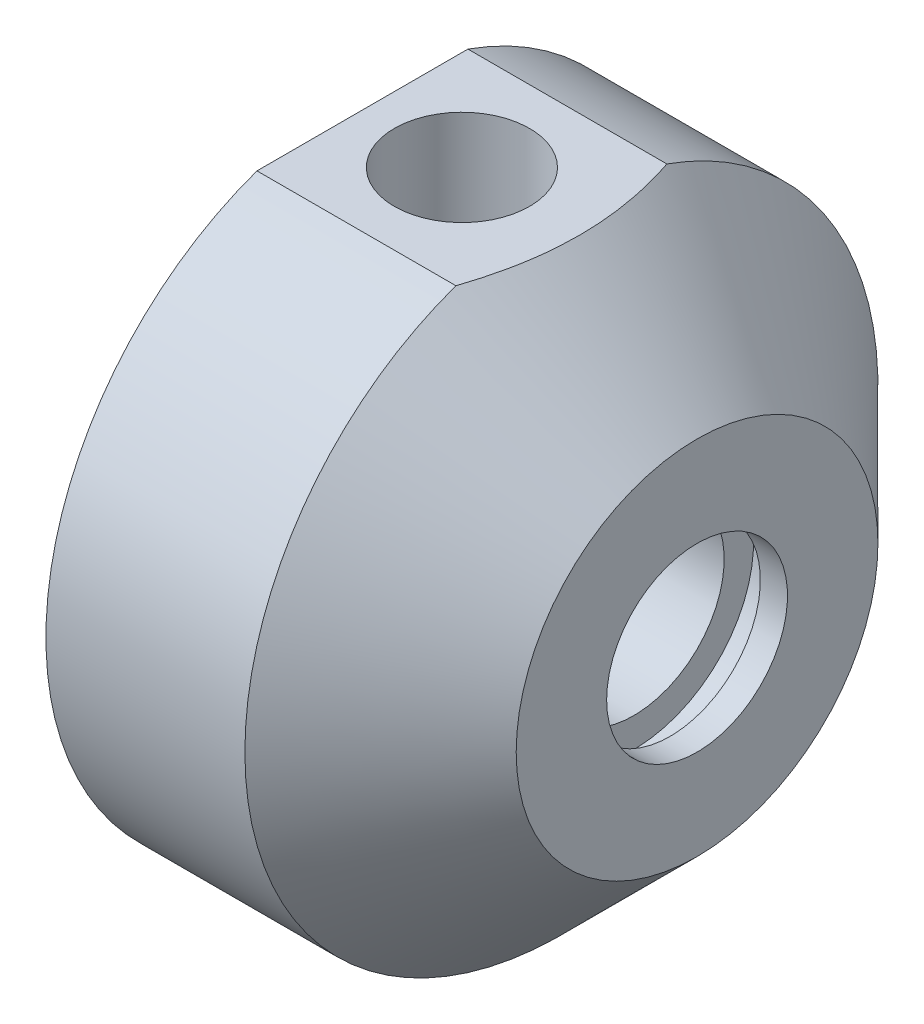
SolidWorks part; units mm, degrees
ref_plane "Plan1" through (0, 0, 0) normal (0, 0, 1) x (1, 0, 0)
ref_plane "Plan2" through (0, 0, 0) normal (0, 1, 0) x (1, 0, 0)
ref_plane "Plan3" through (0, 0, 0) normal (1, 0, 0) x (0, 0, -1)
sketch "Esquisse1" plane through (0, 0, 0) normal (0, 0, 1) x (1, 0, 0)
  line L0 (-21, 0) -> (25, 0) construction
  line L1 (-26, 16) -> (-26, 20)
  line L2 (-26, 20) -> (-23, 20)
  line L3 (-23, 20) -> (-23, 18.5)
  line L4 (-23, 18.5) -> (-20.4, 18.5)
  line L5 (-20.4, 18.5) -> (-20.4, 20)
  line L6 (-20.4, 20) -> (-16, 20)
  line L7 (-16, 20) -> (-16, 35)
  line L8 (-16, 35) -> (6, 35)
  line L9 (6, 35) -> (21, 20)
  line L10 (21, 20) -> (21, 10)
  line L11 (21, 10) -> (18, 10)
  line L12 (18, 10) -> (18, 13.25)
  line L13 (18, 13.25) -> (14, 13.25)
  line L14 (14, 13.25) -> (14, 10)
  line L15 (14, 10) -> (3.7321, 10)
  line L16 (3.7321, 10) -> (2, 13)
  line L17 (-23, 13) -> (2, 13)
  line L19 (-23, 13) -> (-26, 16)
  dimension "D1" = 20
  dimension "D2" = 13
  dimension "D3" = 35
  dimension "D4" = 3
  dimension "D5" = 3
  dimension "D6" = 2.6
  dimension "D7" = 10
  dimension "D8" = 22
  dimension "D9" = 45
  dimension "D10" = 47
  dimension "D11" = 18.5
  dimension "D12" = 3
  dimension "D13" = 4
  dimension "D14" = 10
  dimension "D15" = 13.25
  dimension "D16" = 28
  dimension "D17" = 45
  dimension "D18" = 60
revolve "Base-Révolution" add sketch "Esquisse1" angle 360 about L0
sketch "Esquisse2" plane through (0, 0, 0) normal (0, 0, 1) x (1, 0, 0)
  line L0 (-31, 33) -> (20, 33)
  line L1 (20, 33) -> (20, 39)
  line L2 (20, 39) -> (-31, 39)
  line L3 (-31, 39) -> (-31, 33)
  dimension "D1" = 33
extrude "Enlèv. mat.-Extru.1" cut sketch "Esquisse2" against normal mid plane 50
sketch "Esquisse3" plane through (0, 33, 0) normal (0, 1, 0) x (-1, 0, 0)
  line L0 (21, 0) -> (-25, 0) construction
  line L1 (16, -11.6619) -> (16, 11.6619) construction
  circle A0 centre (5, 0) radius 7.475
  dimension "D1" = 14.95
  dimension "D2" = 11
extrude "Enlèv. mat.-Extru.2" cut sketch "Esquisse3" against normal up to next
sketch "Esquisse4" plane through (-16, 0, 0) normal (-1, 0, 0) x (0, 0, 1)
  line L0 (0, 0) -> (32.1403, -32.1403) construction
  line L1 (0, 0) -> (39, 0) construction
  circle A0 centre (19.799, -19.799) radius 3
  dimension "D2" = 6
  dimension "D1" = 45
  dimension "D3" = 28
extrude "Enlèv. mat.-Extru.3" cut sketch "Esquisse4" against normal blind 20
pattern_circular "Répétition circulaire1" count 4 every 90 about axis through (-21, 0, 0) along (1, 0, 0)
ref_plane "Plan4" through (0, 0, -35) normal (0, 0, 1) x (1, 0, 0)
sketch "Esquisse7" plane through (0, 0, -35) normal (0, 0, 1) x (1, 0, 0)
  line L0 (-5, -41.2318) -> (-5, -22.5394) construction
  circle A0 centre (-5, 0.3496) radius 3
  dimension "D1" = 6
extrude "Enlèv. mat.-Extru.5" cut sketch "Esquisse7" along normal blind 11
sketch "Esquisse8" plane through (0, 0, -24) normal (0, 0, -1) x (-1, 0, 0)
  circle A0 centre (5, 0.3496) radius 1
  dimension "D1" = 2
extrude "Enlèv. mat.-Extru.6" cut sketch "Esquisse8" against normal up to next
